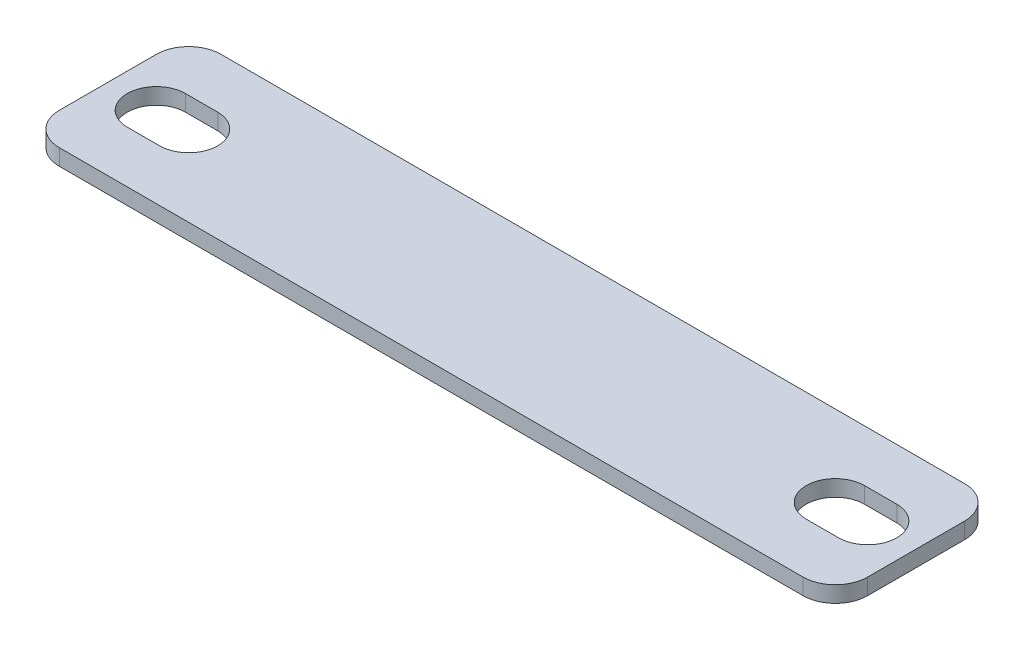
SolidWorks part; units mm, degrees
ref_plane "Front Plane" through (0, 0, 0) normal (0, 0, 1) x (1, 0, 0)
ref_plane "Top Plane" through (0, 0, 0) normal (0, 1, 0) x (1, 0, 0)
ref_plane "Right Plane" through (0, 0, 0) normal (1, 0, 0) x (0, 0, -1)
sketch "Sketch1" plane through (0, 0, 0) normal (0, 1, 0) x (1, 0, 0)
  line L0 (-26.67, 0) -> (26.67, 0) construction
  line L1 (-31.75, -6.35) -> (31.75, -6.35)
  line L2 (-31.75, -6.35) -> (-31.75, 6.35)
  line L3 (-31.75, 6.35) -> (31.75, 6.35)
  line L4 (31.75, -6.35) -> (31.75, 6.35)
  line L5 (-27.94, 0) -> (-25.4, 0) construction
  line L8 (25.4, 0) -> (27.94, 0) construction
  line L9 (25.4, 2.286) -> (27.94, 2.286)
  line L10 (25.4, -2.286) -> (27.94, -2.286)
  line L11 (-27.94, 2.286) -> (-25.4, 2.286)
  line L12 (-27.94, -2.286) -> (-25.4, -2.286)
  arc A4 (25.4, 2.286) -> (25.4, -2.286) centre (25.4, 0) ccw
  arc A5 (27.94, -2.286) -> (27.94, 2.286) centre (27.94, 0) ccw
  arc A6 (-27.94, 2.286) -> (-27.94, -2.286) centre (-27.94, 0) ccw
  arc A7 (-25.4, -2.286) -> (-25.4, 2.286) centre (-25.4, 0) ccw
  point P4 (0, 6.35)
  point P6 (-31.75, 0)
  point P11 (0, 0)
  point P12 (-26.67, 0)
  point P18 (26.67, 0)
  dimension "D3" = 2.286
  dimension "D1" = 12.7
  dimension "D2" = 63.5
  dimension "D4" = 53.34
  dimension "D5" = 2.54
extrude "Boss-Extrude1" add sketch "Sketch1" along normal blind 1.27
fillet "Fillet1" radius 2.54 4 edges at (31.75, 0.635, -6.35) (31.75, 0.635, 6.35) (-31.75, 0.635, -6.35) (-31.75, 0.635, 6.35)
